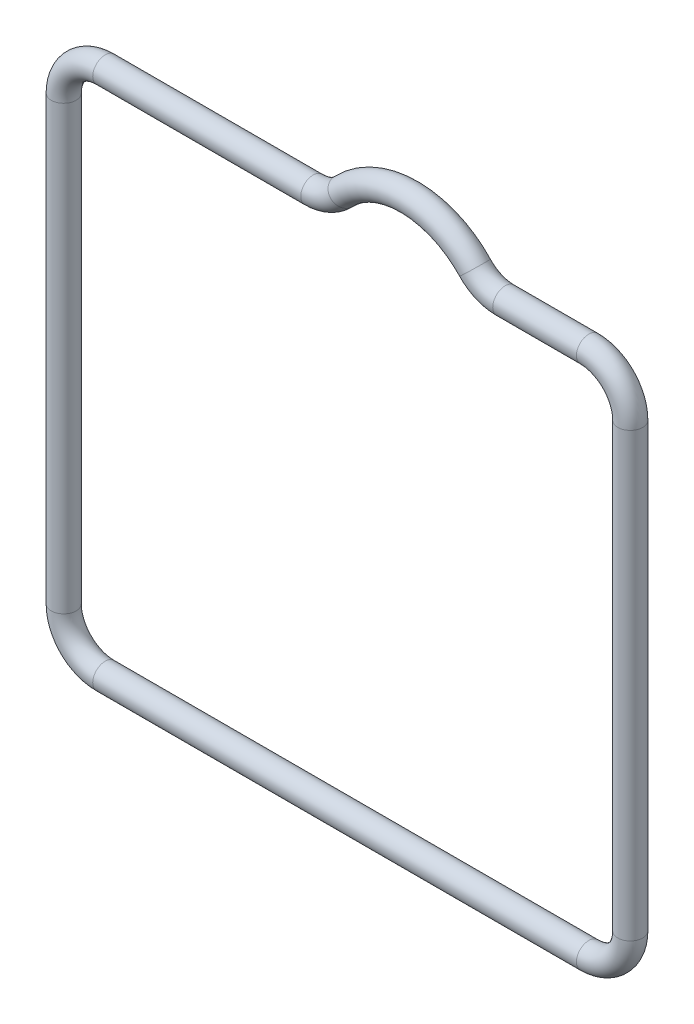
SolidWorks part; units mm, degrees
ref_plane "Спереди" through (0, 0, 0) normal (0, 0, 1) x (1, 0, 0)
ref_plane "Сверху" through (0, 0, 0) normal (0, 1, 0) x (1, 0, 0)
ref_plane "Справа" through (0, 0, 0) normal (1, 0, 0) x (0, 0, -1)
sketch "Эскиз1" plane through (0, 0, 0) normal (0, 0, 1) x (1, 0, 0)
  line L0 (0, 3) -> (0, 35)
  line L1 (3, 38) -> (18.0538, 38)
  line L3 (31.9462, 38) -> (38, 38)
  line L4 (41, 35) -> (41, 3)
  line L5 (38, 0) -> (3, 0)
  arc A0 (20.2377, 38.9432) -> (29.7623, 38.9432) centre (25, 34.4583) cw
  arc A1 (18.0538, 38) -> (20.2377, 38.9432) centre (18.0538, 41) ccw
  arc A2 (29.7623, 38.9432) -> (31.9462, 38) centre (31.9462, 41) ccw
  arc A3 (38, 38) -> (41, 35) centre (38, 35) cw
  arc A4 (41, 3) -> (38, 0) centre (38, 3) cw
  arc A5 (0, 3) -> (3, 0) centre (3, 3) ccw
  arc A6 (0, 35) -> (3, 38) centre (3, 35) cw
  point P8 (25, 41)
  point P11 (19.5, 38)
  point P14 (30.5, 38)
  point P21 (0, 0)
  point P24 (0, 38)
  dimension "D5" = 3
  dimension "D6" = 3
  dimension "D1" = 41
  dimension "D2" = 38
  dimension "D3" = 16
  dimension "D4" = 11
ref_plane "Плоскость1" through (0, 3, 0) normal (0, 1, 0) x (1, 0, 0)
sketch "Эскиз3" plane through (0, 3, 0) normal (0, 1, 0) x (1, 0, 0)
  circle A0 centre (0, 0) radius 0.9
  dimension "D1" = 1.8
sweep "По траектории2" add profiles "Эскиз3" path "Эскиз1"
